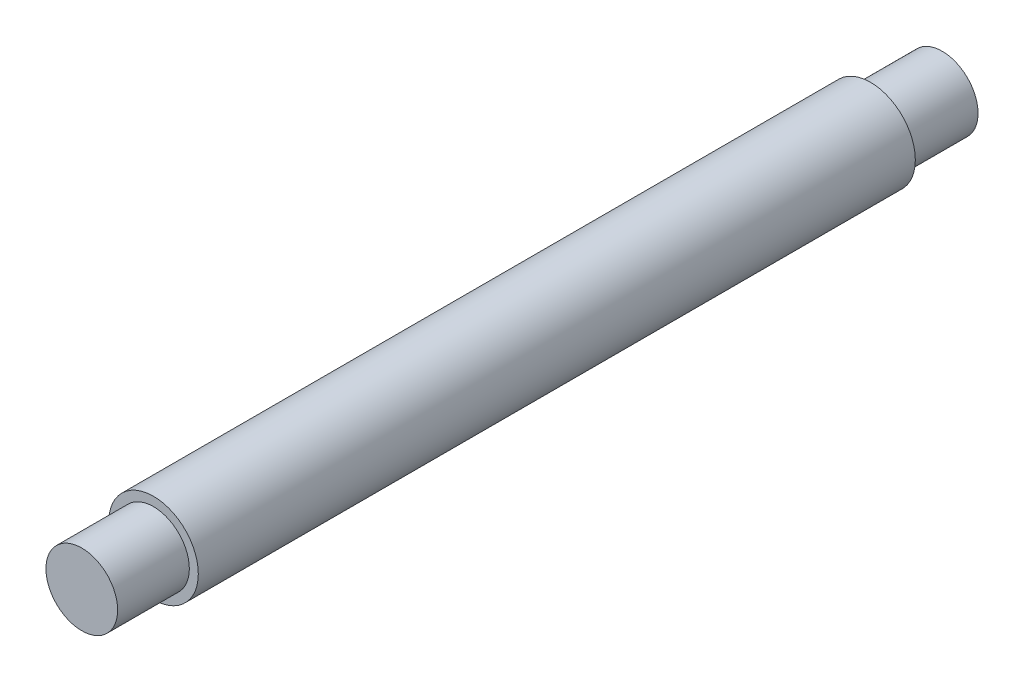
SolidWorks part; units mm, degrees
ref_plane "Front Plane" through (0, 0, 0) normal (0, 0, 1) x (1, 0, 0)
ref_plane "Top Plane" through (0, 0, 0) normal (0, 1, 0) x (1, 0, 0)
ref_plane "Right Plane" through (0, 0, 0) normal (1, 0, 0) x (0, 0, -1)
sketch "Sketch1" plane through (0, 0, 0) normal (0, 0, 1) x (1, 0, 0)
  circle A0 centre (-5.4934, 5.7047) radius 6.35
  dimension "D1" = 12.7
extrude "Boss-Extrude2" add sketch "Sketch1" along normal blind 101.6
sketch "Sketch5" plane through (0, 0, 101.6) normal (0, 0, 1) x (1, 0, 0)
  circle A3 centre (-5.4934, 5.7047) radius 5.08
  dimension "D1" = 10.16
extrude "Boss-Extrude14" add sketch "Sketch5" along normal blind 10.16
sketch "Sketch9" plane through (0, 0, 0) normal (0, 0, -1) x (-1, 0, 0)
  circle A2 centre (5.4934, 5.7047) radius 5.08
  circle A3 centre (5.4934, 5.7047) radius 5.08
  dimension "D1" = 1.27
extrude "Boss-Extrude15" add sketch "Sketch9" along normal blind 10.16
